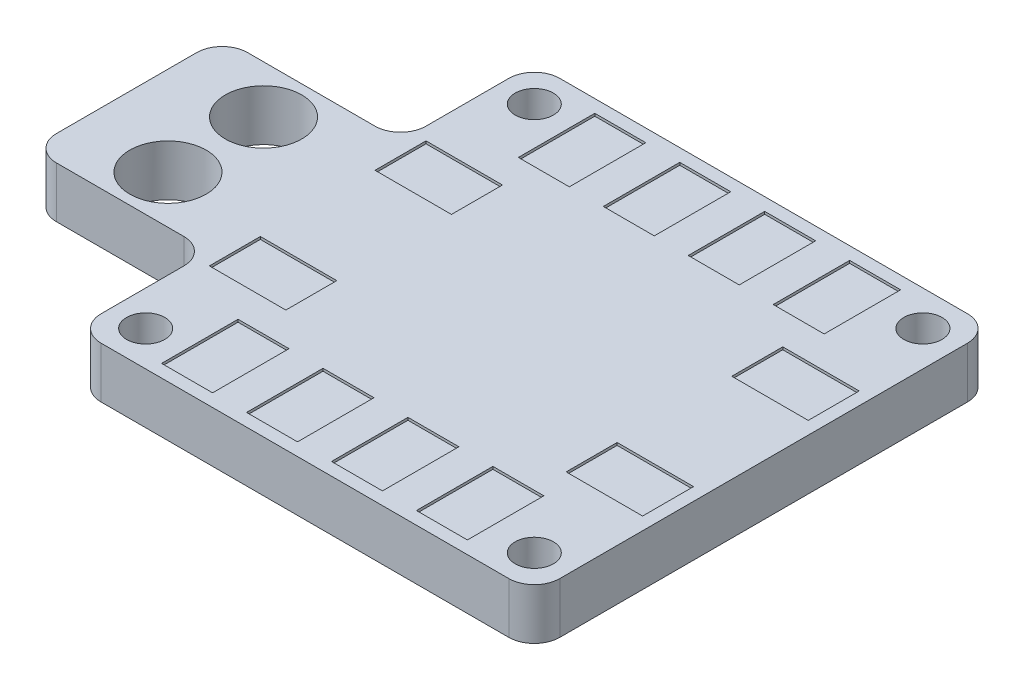
SolidWorks part; units mm, degrees
ref_plane "Front Plane" through (0, 0, 0) normal (0, 0, 1) x (1, 0, 0)
ref_plane "Top Plane" through (0, 0, 0) normal (0, 1, 0) x (1, 0, 0)
ref_plane "Right Plane" through (0, 0, 0) normal (1, 0, 0) x (0, 0, -1)
sketch "Sketch1" plane through (0, 0, 0) normal (0, 1, 0) x (1, 0, 0)
  line L0 (-11, 7.5) -> (-11, 18)
  line L1 (-25, 18) -> (25, 18)
  line L2 (-25, 18) -> (-25, -18)
  line L3 (-25, -18) -> (25, -18)
  line L4 (25, 18) -> (25, -18)
  line L5 (-25, 18) -> (25, -18) construction
  line L6 (-25, -18) -> (25, 18) construction
  line L7 (-25, 7.5) -> (-11, 7.5)
  line L8 (-25, 7.5) -> (-25, -7.5)
  line L9 (-25, -7.5) -> (-11, -7.5)
  line L10 (-11, 7.5) -> (-11, -7.5)
  line L11 (-11, -7.5) -> (-11, -18)
  point P0 (0, 0)
  point P10 (-11, 0)
  dimension "D1" = 36
  dimension "D2" = 50
  dimension "D3" = 36
  dimension "D4" = 15
extrude "Boss-Extrude1" add sketch "Sketch1" along normal blind 4 contours L10 L11 L3 L4 L1 L0 | L10 L7 L2 L9
sketch "Sketch2" plane through (0, 4, 0) normal (0, 1, 0) x (1, 0, 0)
  line L0 (-25, 0) -> (25, 0) construction
  line L1 (-25, 7.5) -> (-25, -7.5) construction
  line L2 (25, 18) -> (25, -18) construction
  line L3 (-25, 7.5) -> (-11, 7.5) construction
  line L4 (-25, 0) -> (-25, 7.5) construction
  line L5 (-11, 18) -> (25, 18) construction
  circle A0 centre (-18, 3.75) radius 3
  circle A1 centre (-8.25, 15.25) radius 1.5
  circle A2 centre (22.25, 15.25) radius 1.5
  circle A3 centre (-18, -3.75) radius 3
  circle A4 centre (22.25, -15.25) radius 1.5
  circle A5 centre (-8.25, -15.25) radius 1.5
  point P10 (-18, 7.5)
  point P11 (-25, 3.75)
  dimension "D1" = 6
  dimension "D2" = 3
  dimension "D5" = 3
  dimension "D6" = 2.75
  dimension "D3" = 2.75
  dimension "D4" = 30.5
extrude "Cut-Extrude1" cut sketch "Sketch2" against normal through all both and the other way through all
fillet "Fillet1" radius 2 8 edges at (25, 2, -18) (-11, 2, -18) (-11, 2, -7.5) (-25, 2, -7.5) (-11, 2, 7.5) (-25, 2, 7.5) (-11, 2, 18) (25, 2, 18)
sketch "Sketch3" plane through (0, 4, 0) normal (0, 1, 0) x (1, 0, 0)
  line L0 (-6.75, 18) -> (-6.75, -18) construction
  line L1 (-5.25, 17) -> (-1.25, 17)
  line L2 (-5.25, 17) -> (-5.25, 11)
  line L3 (-5.25, 11) -> (-1.25, 11)
  line L4 (-1.25, 17) -> (-1.25, 11)
  line L5 (-9, 18) -> (23, 18) construction
  line L6 (-9, -18) -> (23, -18) construction
  line L7 (20.75, 18) -> (20.75, -18) construction
  circle A0 centre (-8.25, 15.25) radius 1.5 construction
  circle A1 centre (22.25, -15.25) radius 1.5 construction
  dimension "D1" = 3
  dimension "D2" = 1
  dimension "D3" = 6
  dimension "D4" = 4
extrude "Cut-Extrude2" cut sketch "Sketch3" against normal blind 0.2 and the other way through all
pattern_linear "LPattern1" count 4 spacing 6.6667 along (1, 0, 0) of "Cut-Extrude2"
mirror "Mirror1" about plane through (0, 0, 0) normal (0, 0, 1) of "LPattern1", "Cut-Extrude2"
sketch "Sketch4" plane through (0, 4, 0) normal (0, 1, 0) x (1, 0, 0)
  line L0 (25, 16) -> (25, -16) construction
  line L1 (18, 8.5) -> (24, 8.5)
  line L2 (18, 8.5) -> (18, 4.5)
  line L3 (18, 4.5) -> (24, 4.5)
  line L4 (24, 8.5) -> (24, 4.5)
  line L5 (14.75, 11) -> (18.75, 11) construction
  line L6 (7, -18) -> (7, 18) construction
  line L7 (-9, -18) -> (23, -18) construction
  line L8 (-9, 18) -> (23, 18) construction
  line L9 (-10, 8.5) -> (-10, 4.5)
  line L10 (-4, 4.5) -> (-10, 4.5)
  line L11 (-4, 8.5) -> (-4, 4.5)
  line L12 (-4, 8.5) -> (-10, 8.5)
  line L13 (-25, 0) -> (0, 0) construction
  line L14 (-25, 5.5) -> (-25, -5.5) construction
  line L15 (-10, -8.5) -> (-10, -4.5)
  line L16 (-4, -8.5) -> (-10, -8.5)
  line L17 (-4, -8.5) -> (-4, -4.5)
  line L18 (-4, -4.5) -> (-10, -4.5)
  line L19 (18, -4.5) -> (24, -4.5)
  line L20 (24, -8.5) -> (24, -4.5)
  line L21 (18, -8.5) -> (24, -8.5)
  line L22 (18, -8.5) -> (18, -4.5)
  dimension "D1" = 4
  dimension "D2" = 6
  dimension "D3" = 1
  dimension "D4" = 2.5
extrude "Cut-Extrude3" cut sketch "Sketch4" against normal blind 0.2 and the other way through all
